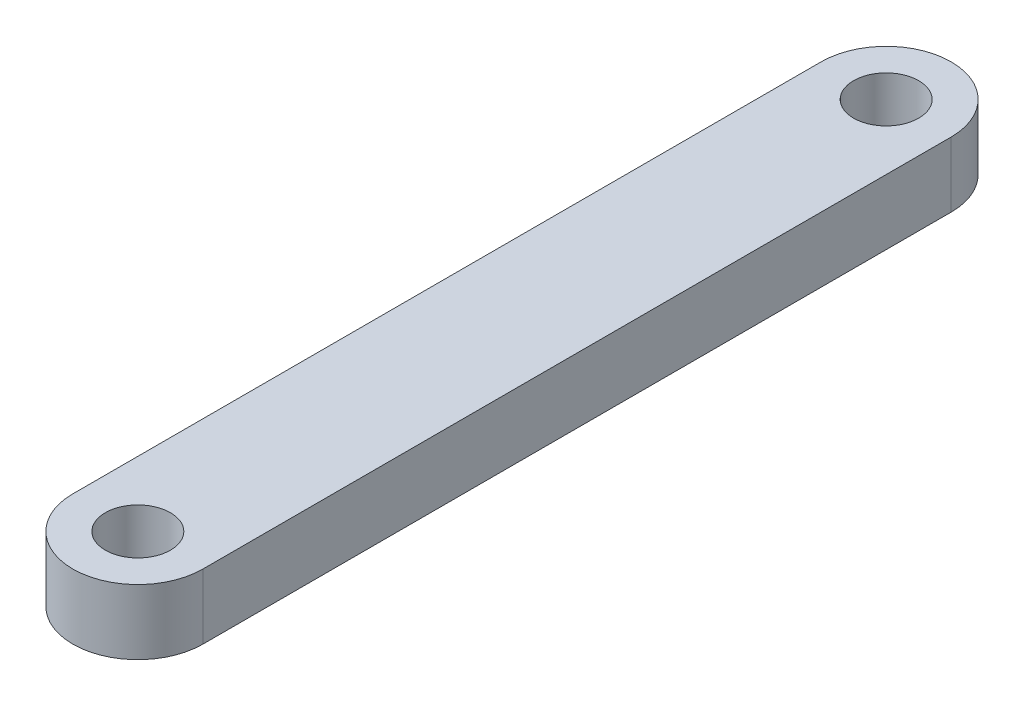
SolidWorks part; units mm, degrees
ref_plane "Front Plane" through (0, 0, 0) normal (0, 0, 1) x (1, 0, 0)
ref_plane "Top Plane" through (0, 0, 0) normal (0, 1, 0) x (1, 0, 0)
ref_plane "Right Plane" through (0, 0, 0) normal (1, 0, 0) x (0, 0, -1)
sketch "Sketch1" plane through (0, 0, 0) normal (0, 1, 0) x (1, 0, 0)
  line L0 (0, 23) -> (0, -23) construction
  line L1 (4, 23) -> (4, -23)
  line L2 (-4, 23) -> (-4, -23)
  arc A0 (4, 23) -> (-4, 23) centre (0, 23) ccw
  arc A1 (-4, -23) -> (4, -23) centre (0, -23) ccw
  circle A2 centre (0, 23) radius 2
  circle A3 centre (0, -23) radius 2
  point P2 (0, 0)
  dimension "D3" = 4
  dimension "D4" = 4
  dimension "D1" = 46
  dimension "D2" = 8
extrude "Boss-Extrude1" add sketch "Sketch1" along normal blind 4
